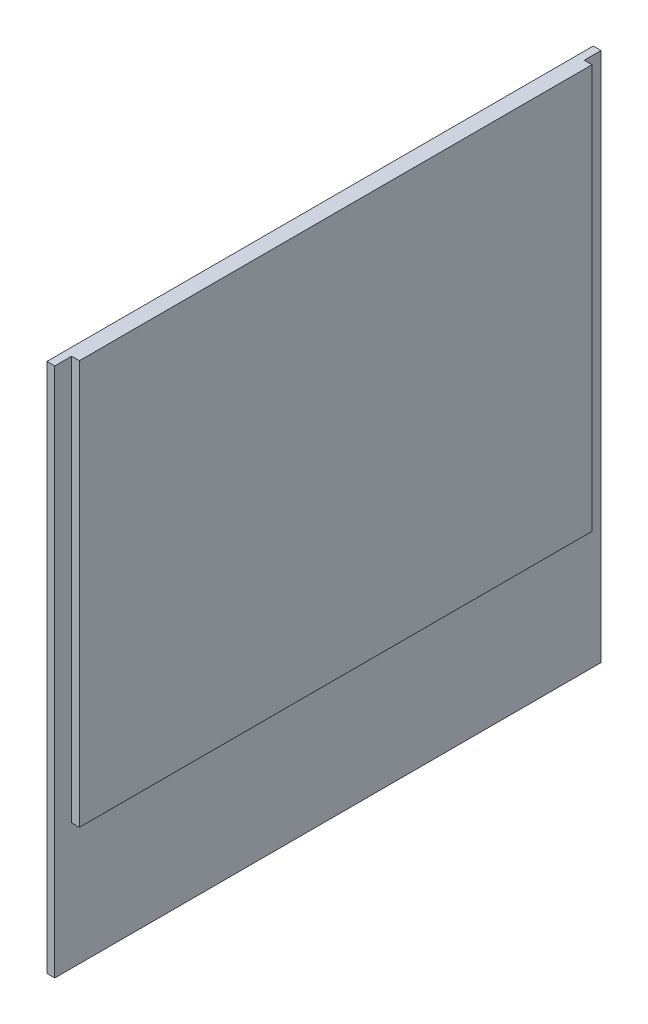
SolidWorks part; units mm, degrees
ref_plane "Front Plane" through (0, 0, 0) normal (0, 0, 1) x (1, 0, 0)
ref_plane "Top Plane" through (0, 0, 0) normal (0, 1, 0) x (1, 0, 0)
ref_plane "Right Plane" through (0, 0, 0) normal (1, 0, 0) x (0, 0, -1)
sketch "Sketch1" plane through (0, 0, 0) normal (1, 0, 0) x (0, 0, -1)
  line L1 (0, 0) -> (111.252, 0)
  line L2 (0, 0) -> (0, 107.95)
  line L3 (0, 107.95) -> (111.252, 107.95)
  line L4 (111.252, 0) -> (111.252, 107.95)
  dimension "D1" = 111.252
  dimension "D2" = 107.95
extrude "Boss-Extrude1" add sketch "Sketch1" along normal blind 1.5875
sketch "Sketch2" plane through (1.5875, 0, 0) normal (1, 0, 0) x (0, 0, -1)
  line L0 (111.252, 107.95) -> (0, 107.95) construction
  line L1 (3.429, 107.95) -> (107.823, 107.95)
  line L2 (3.429, 107.95) -> (3.429, 25.654)
  line L3 (3.429, 25.654) -> (107.823, 25.654)
  line L4 (107.823, 107.95) -> (107.823, 25.654)
  line L5 (0, 0) -> (111.252, 0) construction
  line L6 (0, 107.95) -> (0, 0) construction
  line L7 (111.252, 0) -> (111.252, 107.95) construction
  dimension "D1" = 25.654
  dimension "D2" = 3.429
  dimension "D3" = 3.429
extrude "Boss-Extrude2" add sketch "Sketch2" along normal blind 1.5875
